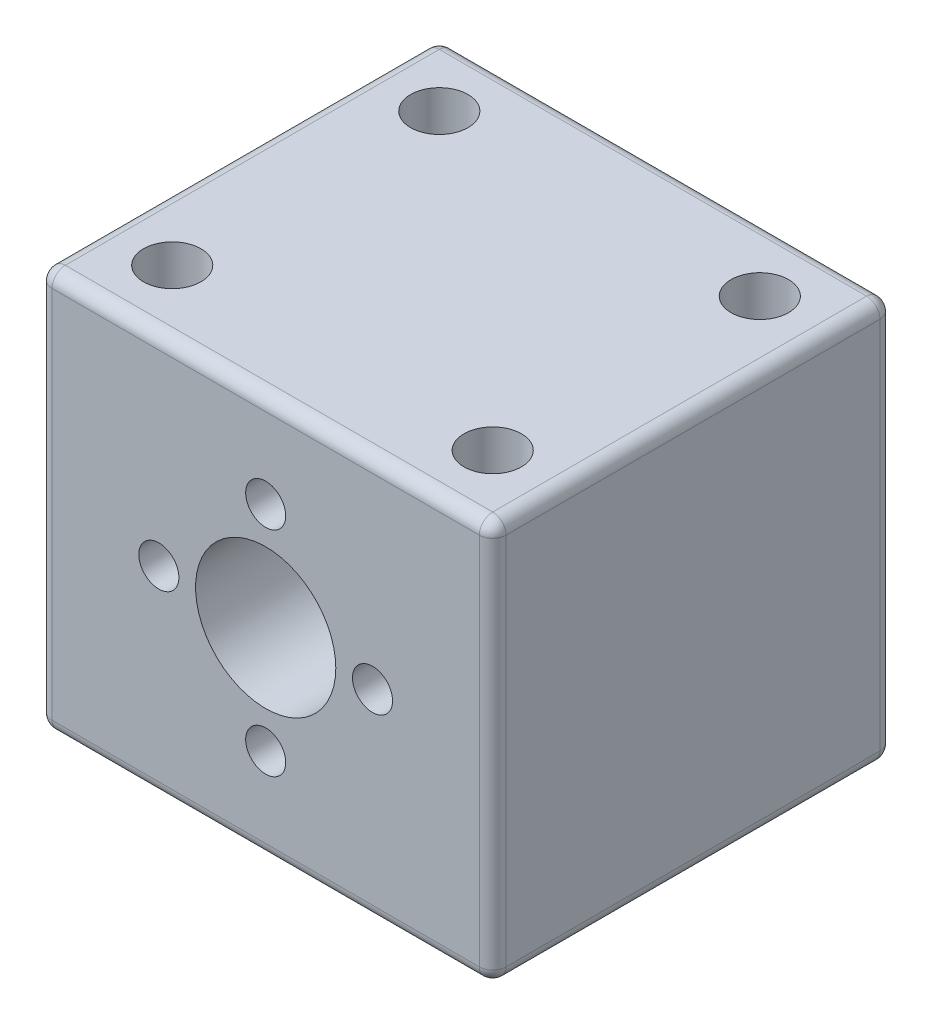
SolidWorks part; units mm, degrees
material "1100-H16 Rod (SS)"
ref_plane "前视基准面" through (0, 0, 0) normal (0, 0, 1) x (1, 0, 0)
ref_plane "上视基准面" through (0, 0, 0) normal (0, 1, 0) x (1, 0, 0)
ref_plane "右视基准面" through (0, 0, 0) normal (1, 0, 0) x (0, 0, -1)
other "Configuration Table"
sketch "Sketch1" plane through (0, 0, 0) normal (0, 0, 1) x (1, 0, 0)
  line L1 (0, 0) -> (34, 0)
  line L2 (0, 0) -> (0, -30)
  line L3 (0, -30) -> (34, -30)
  line L4 (34, 0) -> (34, -30)
  dimension "D1" = 30
  dimension "D2" = 34
extrude "Boss-Extrude1" add sketch "Sketch1" along normal blind 30
sketch "Sketch2" plane through (0, 0, 30) normal (0, 0, 1) x (1, 0, 0)
  line L0 (34, 0) -> (0, 0) construction
  line L1 (0, 0) -> (0, -30) construction
  circle A0 centre (17, -15) radius 5.25
  circle A1 centre (17, -7) radius 1.5
  circle A2 centre (25, -15) radius 1.5
  circle A3 centre (17, -23) radius 1.5
  circle A4 centre (9, -15) radius 1.5
  point P7 (17, 0)
  point P11 (0, -15)
  point P19 (17, -15)
  dimension "D1" = 10.5
  dimension "D2" = 3
  dimension "D3" = 8
  dimension "D4" = 4
extrude "Cut-Extrude1" cut sketch "Sketch2" against normal blind 30 contours A0
sketch "Sketch3" plane through (0, 0, 30) normal (0, 0, 1) x (1, 0, 0)
  circle A1 centre (25, -15) radius 1.5
  circle A2 centre (25, -15) radius 1.5
  circle A3 centre (17, -7) radius 1.5
  circle A4 centre (17, -7) radius 1.5
  circle A7 centre (9, -15) radius 1.5
  circle A8 centre (9, -15) radius 1.5
  circle A9 centre (17, -23) radius 1.5
  circle A10 centre (17, -23) radius 1.5
  dimension "D1" = 0
  dimension "D2" = 0
  dimension "D4" = 0
  dimension "D5" = 0
extrude "Cut-Extrude2" cut sketch "Sketch3" against normal blind 15
fillet "Fillet1" radius 1 12 edges at (0, -15, 0) (17, -30, 0) (34, -15, 0) (17, 0, 0) (0, -15, 30) (17, -30, 30) (34, -15, 30) (34, 0, 15) (34, -30, 15) (0, -30, 15) (0, 0, 15) (17, 0, 30)
sketch "Sketch4" plane through (0, 0, 0) normal (0, 1, 0) x (1, 0, 0)
  line L0 (17, -2) -> (17, -21.8684) construction
  line L2 (33, -1) -> (1, -1) construction
  line L3 (6.8854, -15) -> (27.0572, -15) construction
  line L4 (33, -29) -> (33, -1) construction
  circle A0 centre (5, -5) radius 2.15
  circle A1 centre (29, -5) radius 2.15
  circle A2 centre (29, -25) radius 2.15
  circle A3 centre (5, -25) radius 2.15
  point P5 (17, -1)
  point P11 (33, -15)
  dimension "D1" = 4.3
  dimension "D2" = 24
  dimension "D3" = 20
extrude "Cut-Extrude3" cut sketch "Sketch4" against normal blind 20
